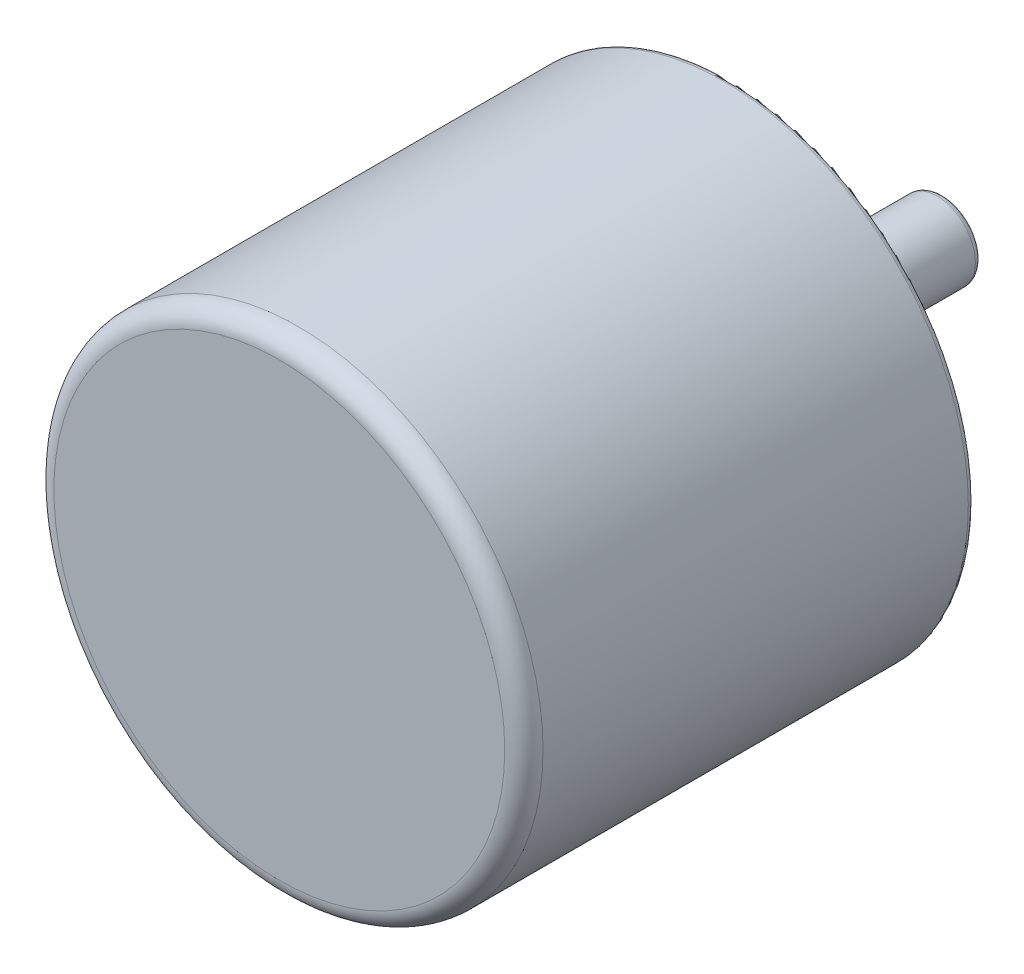
SolidWorks part; units mm, degrees
ref_plane "Front Plane" through (0, 0, 0) normal (0, 0, 1) x (1, 0, 0)
ref_plane "Top Plane" through (0, 0, 0) normal (0, 1, 0) x (1, 0, 0)
ref_plane "Right Plane" through (0, 0, 0) normal (1, 0, 0) x (0, 0, -1)
sketch "Sketch1" plane through (0, 0, 0) normal (0, 0, 1) x (1, 0, 0)
  circle A0 centre (0, 0) radius 19.15
  dimension "D1" = 38.3
extrude "Boss-Extrude1" add sketch "Sketch1" along normal blind 35.3
sketch "Sketch2" plane through (0, 0, 0) normal (0, 0, -1) x (-1, 0, 0)
  circle A0 centre (0, 0) radius 10
  circle A1 centre (0, 0) radius 7.5
  dimension "D1" = 15
  dimension "D2" = 20
extrude "Boss-Extrude2" add sketch "Sketch2" along normal blind 4.7
sketch "Sketch3" plane through (0, 0, 0) normal (0, 0, -1) x (-1, 0, 0)
  circle A0 centre (0, 0) radius 3
  dimension "D1" = 6
extrude "Boss-Extrude3" add sketch "Sketch3" along normal blind 16.7
sketch "Sketch4" plane through (0, 0, 0) normal (0, 0, -1) x (-1, 0, 0)
  line L0 (0, 0) -> (0, 19.15) construction
  line L1 (0, 0) -> (16.5844, -9.575) construction
  line L2 (0, 0) -> (-16.5844, -9.575) construction
  line L3 (0, 0) -> (-5.3591, 18.3849) construction
  line L4 (0, 14.15) -> (-3.9598, 13.5846) construction
  line L5 (0, 0) -> (18.6013, -4.5513) construction
  line L6 (0, 0) -> (-13.2422, -13.8335) construction
  circle A4 centre (0, 0) radius 19.15 construction
  circle A5 centre (0, 0) radius 14.15 construction
  circle A6 centre (-3.9598, 13.5846) radius 1.0085
  circle A7 centre (0, 14.15) radius 1.0263
  circle A8 centre (12.2543, -7.075) radius 1.0263
  circle A9 centre (13.7446, -3.363) radius 1.0085
  circle A10 centre (-12.2543, -7.075) radius 1.0263
  circle A11 centre (-9.7847, -10.2216) radius 1.0085
  point P11 (0, 0)
  point P16 (-12.2543, -7.075)
  point P17 (-9.7847, -10.2216)
  point P19 (0, 0)
  point P20 (12.2543, -7.075)
  point P21 (13.7446, -3.363)
  point P35 (0, 0)
  dimension "D2" = 28.3
  dimension "D3" = 4
  dimension "D1" = 3
  dimension "D4" = 3
  dimension "D5" = 3
extrude "Cut-Extrude1" cut sketch "Sketch4" against normal blind 6.8
fillet "Fillet1" radius 1.5 1 edges at (19.15, 0, 35.3)
fillet "Fillet2" radius 0.5 1 edges at (-3, 0, -16.7)
fillet "Fillet3" radius 0.5 1 edges at (-10, 0, -4.7)
fillet "Fillet4" radius 0.5 1 edges at (19.15, 0, 0)
